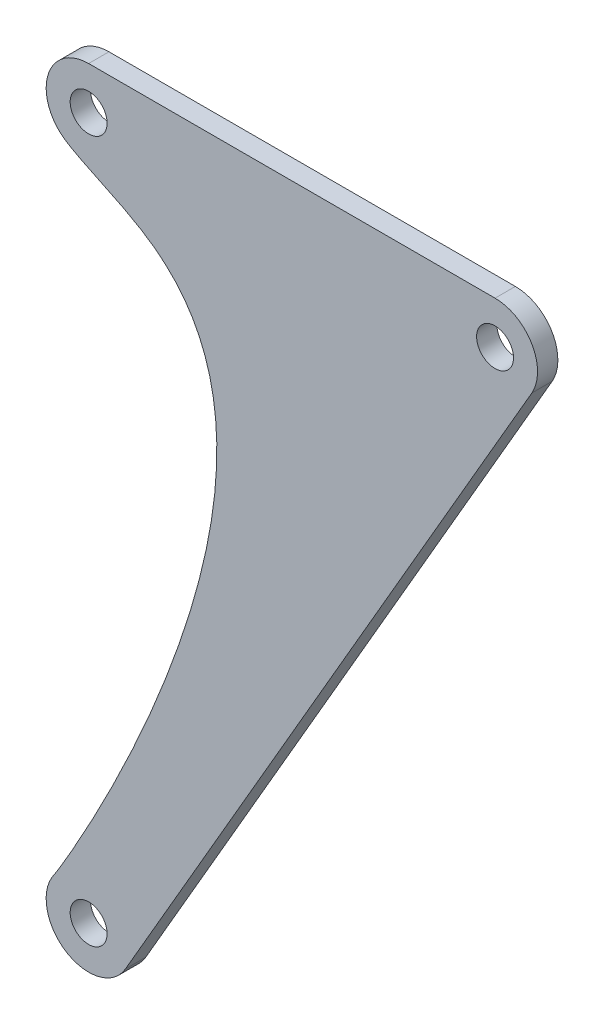
SolidWorks part; units mm, degrees
material "1.0490 (S275N)"
ref_plane "Front Plane" through (0, 0, 0) normal (0, 0, 1) x (1, 0, 0)
ref_plane "Top Plane" through (0, 0, 0) normal (0, 1, 0) x (1, 0, 0)
ref_plane "Right Plane" through (0, 0, 0) normal (1, 0, 0) x (0, 0, -1)
sketch "Sketch1" plane through (0, 0, 0) normal (0, 0, 1) x (1, 0, 0)
  line L0 (-110, 11.5) -> (0, 11.5)
  line L1 (9.9524, -5.7619) -> (-100.0476, -195.7619)
  circle A0 centre (0, 0) radius 5
  arc A1 (-110, 11.5) -> (-117.5827, -8.646) centre (-110, 0) ccw
  arc A2 (-119.2404, -183.1543) -> (-100.0476, -195.7619) centre (-110, -190) ccw
  circle A3 centre (-110, -190) radius 5
  circle A4 centre (-110, 0) radius 5
  arc A5 (9.9524, -5.7619) -> (0, 11.5) centre (0, 0) ccw
  spline S0 degree 3 poles (-117.5827, -8.646) (-113.5006, -12.226) (-89.3431, -20.2497) (-54.53, -76.6995) (-117.5178, -180.8291) (-119.2404, -183.1543) knots 0 0 0 0 0.138536 0.282876 1 1 1 1
  point P16 (-77.0806, -45.924)
  dimension "D1" = 10
  dimension "D2" = 10
  dimension "D3" = 10
  dimension "D4" = 23
  dimension "D5" = 23
  dimension "D6" = 23
  dimension "D7" = 110
  dimension "D8" = 190
extrude "Boss-Extrude1" add sketch "Sketch1" along normal mid plane 5.5
